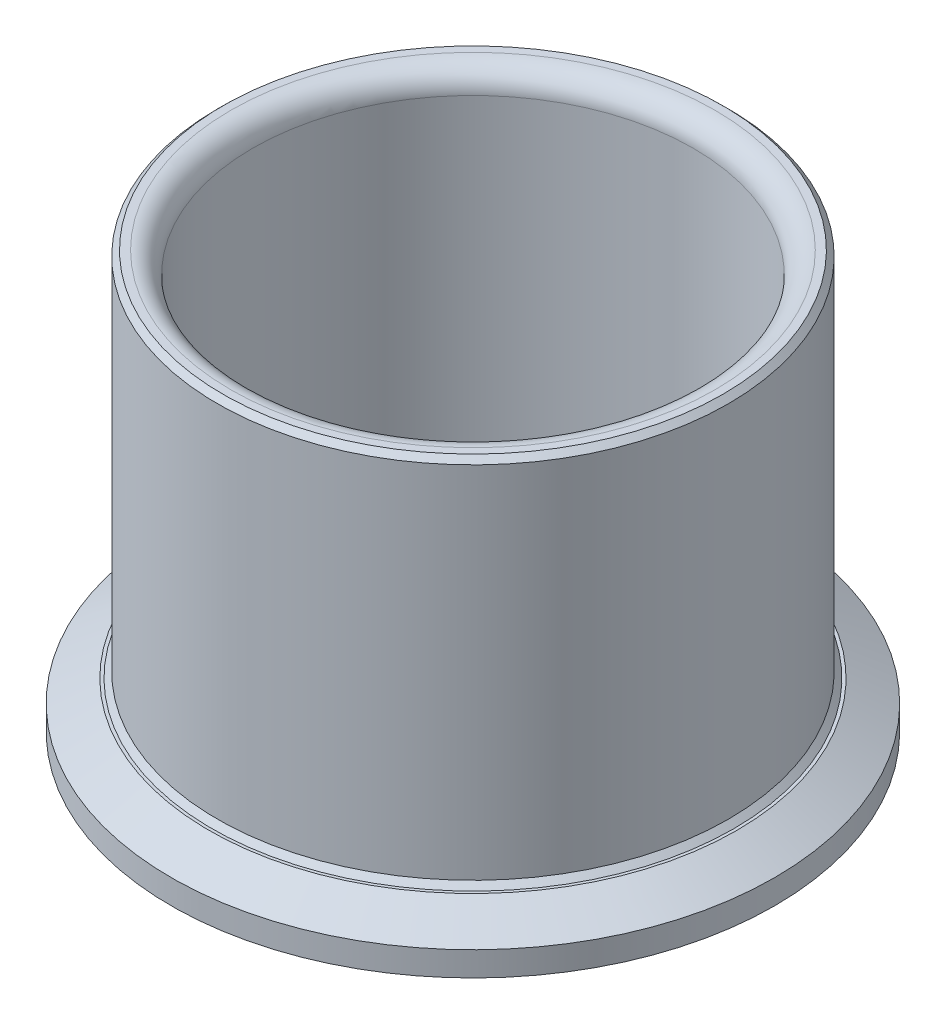
SolidWorks part; units mm, degrees
ref_plane "Plan de face" through (0, 0, 0) normal (0, 0, 1) x (1, 0, 0)
ref_plane "Plan de dessus" through (0, 0, 0) normal (0, 1, 0) x (1, 0, 0)
ref_plane "Plan de droite" through (0, 0, 0) normal (1, 0, 0) x (0, 0, -1)
sketch "Sketch2" plane through (0, 0, 0) normal (0, 0, 1) x (1, 0, 0)
  line L0 (0, 0) -> (0, 58.15)
  line L1 (0, 58.15) -> (-35, 58.15)
  line L2 (-35, 58.15) -> (-35, 7.35)
  line L3 (-35, 7.35) -> (-41.35, 7.35)
  line L4 (-41.35, 7.35) -> (-41.35, 1)
  line L5 (-41.35, 1) -> (-31.75, 1)
  line L6 (-31.75, 1) -> (-31.75, 0)
  line L7 (-31.75, 0) -> (0, 0)
  dimension "D1" = 50.8
  dimension "D2" = 35
  dimension "D3" = 6.35
  dimension "D4" = 1
  dimension "D5" = 31.75
revolve "Revolve1" add sketch "Sketch2" angle 360 about L0
sketch "Sketch3" plane through (0, 58.15, 0) normal (0, 1, 0) x (1, 0, 0)
  circle A0 centre (0, 0) radius 30.175
  dimension "D1" = 60.35
extrude "Cut-Extrude1" cut sketch "Sketch3" against normal through all
chamfer "Chamfer1" distance 0.75 angle 45 2 edges at (35, 58.15, 0) (35, 7.35, 0)
chamfer "Chamfer2" distance 3 angle 60 1 edges at (41.35, 7.35, 0)
fillet "Fillet1" radius 3 1 edges at (-30.175, 58.15, 0)
